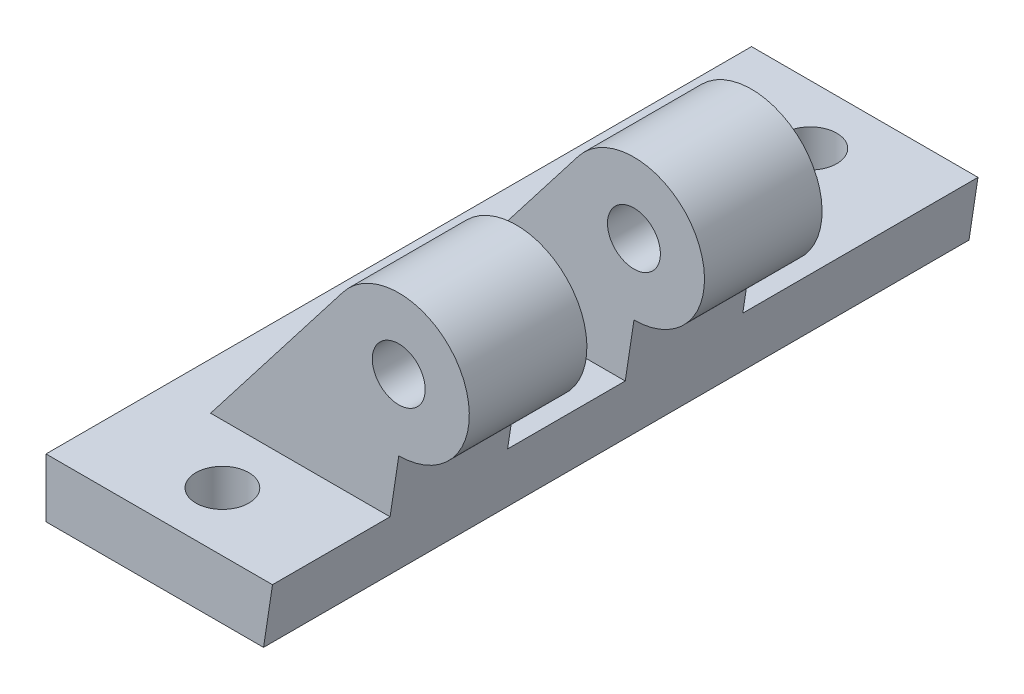
SolidWorks part; units mm, degrees
ref_plane "Front Plane" through (0, 0, 0) normal (0, 0, 1) x (1, 0, 0)
ref_plane "Top Plane" through (0, 0, 0) normal (0, 1, 0) x (1, 0, 0)
ref_plane "Right Plane" through (0, 0, 0) normal (1, 0, 0) x (0, 0, -1)
sketch "Sketch1" plane through (0, 0, 0) normal (0, 1, 0) x (1, 0, 0)
  line L0 (0, 30) -> (0, -30) construction
  line L1 (-10, -30) -> (10, -30)
  line L2 (-10, -30) -> (-10, 30)
  line L3 (-10, 30) -> (10, 30)
  line L4 (10, -30) -> (10, 30)
  line L5 (-10, -30) -> (10, 30) construction
  line L6 (-10, 30) -> (10, -30) construction
  circle A0 centre (0, 25) radius 2.25
  circle A1 centre (0, -25) radius 2.25
  point P0 (0, 0)
  dimension "D3" = 5
  dimension "D4" = 4.5
  dimension "D5" = 5
  dimension "D6" = 4.5
  dimension "D1" = 20
  dimension "D2" = 60
extrude "Boss-Extrude1" add sketch "Sketch1" along normal blind 5
ref_plane "Plane1" through (0, 0, 20) normal (0, 0, 1) x (1, 0, 0)
ref_plane "Plane2" through (0, 0, -10) normal (0, 0, -1) x (-1, 0, 0)
sketch "Sketch2" plane through (0, 0, 20) normal (0, 0, 1) x (1, 0, 0)
  line L0 (10, 5) -> (10, 0) construction
  line L1 (10, 9.8653) -> (10, 5)
  line L2 (10, 5) -> (-6, 5)
  line L3 (-10, 5) -> (10, 5) construction
  line L4 (-6, 5) -> (5.2557, 19.5384)
  circle A0 centre (10, 15.8653) radius 2.25
  arc A1 (10, 9.8653) -> (5.2557, 19.5384) centre (10, 15.8653) ccw
  dimension "D1" = 4.5
  dimension "D2" = 12
  dimension "D3" = 0
  dimension "D4" = 16
extrude "Boss-Extrude2" add sketch "Sketch2" against normal blind 10
sketch "Sketch3" plane through (0, 0, -10) normal (0, 0, -1) x (-1, 0, 0)
  line L0 (-10, 9.8653) -> (-10, 5)
  line L1 (-10, 5) -> (6, 5)
  line L2 (6, 5) -> (-5.2934, 19.5866)
  circle A0 centre (-10, 15.8653) radius 2.25
  arc A2 (-5.2934, 19.5866) -> (-10, 9.8653) centre (-10, 15.8653) ccw
  dimension "D1" = 4.5
extrude "Boss-Extrude3" add sketch "Sketch3" against normal blind 10
sketch "Sketch5" plane through (0, 0, -30) normal (0, 0, -1) x (-1, 0, 0)
  line L0 (-10, 9.8653) -> (-10, 0)
  line L1 (-10, 0) -> (-8.5, 0)
  line L2 (-10, 0) -> (10, 0) construction
  line L3 (-8.5, 0) -> (-10, 9.8653)
  dimension "D1" = 1.5
extrude "Cut-Extrude1" cut sketch "Sketch5" against normal through all
